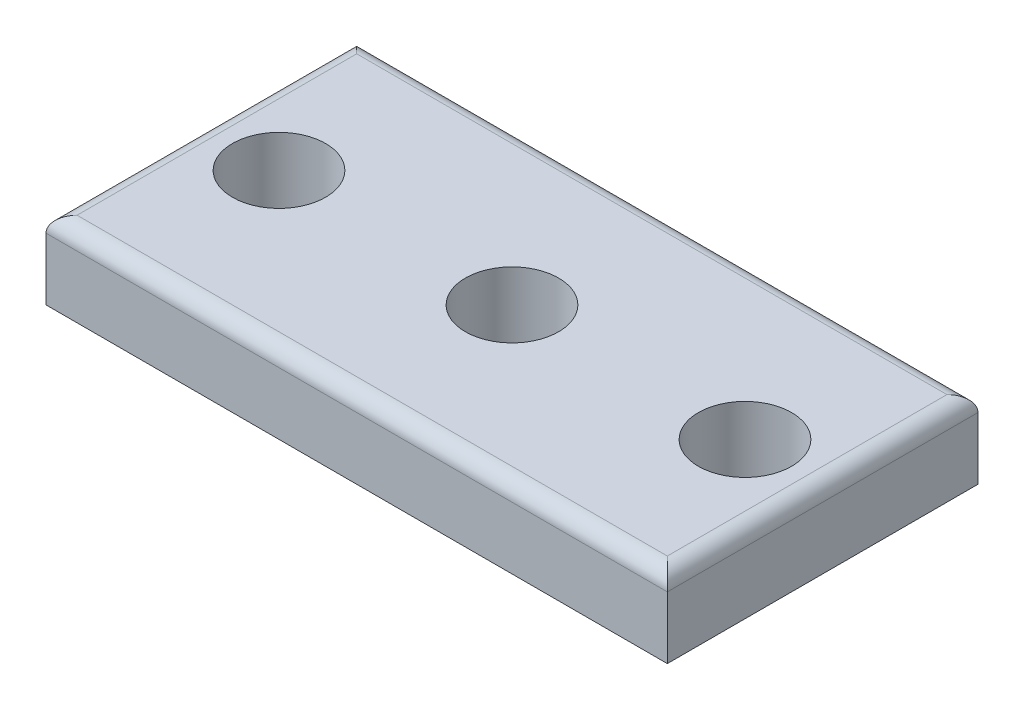
SolidWorks part; units mm, degrees
ref_plane "Front Plane" through (0, 0, 0) normal (0, 0, 1) x (1, 0, 0)
ref_plane "Top Plane" through (0, 0, 0) normal (0, 1, 0) x (1, 0, 0)
ref_plane "Right Plane" through (0, 0, 0) normal (1, 0, 0) x (0, 0, -1)
sketch "Sketch1" plane through (0, 0, 0) normal (0, 1, 0) x (1, 0, 0)
  line L0 (0, -55) -> (0, 55) construction
  line L1 (-20, -10) -> (20, -10)
  line L2 (-20, -10) -> (-20, 10)
  line L3 (-20, 10) -> (20, 10)
  line L4 (20, -10) -> (20, 10)
  line L5 (-55, 0) -> (55, 0) construction
  circle A0 centre (-15, 0) radius 3
  circle A1 centre (15, 0) radius 3
  circle A2 centre (0, 0) radius 3
  dimension "D5" = 6
  dimension "D1" = 40
  dimension "D2" = 20
  dimension "D3" = 20
  dimension "D4" = 10
  dimension "D6" = 15
  dimension "D7" = 15
extrude "Boss-Extrude1" add sketch "Sketch1" along normal blind 5
fillet "Fillet1" radius 1 4 edges at (-20, 5, 0) (20, 5, 0) (0, 5, 10) (0, 5, -10)
